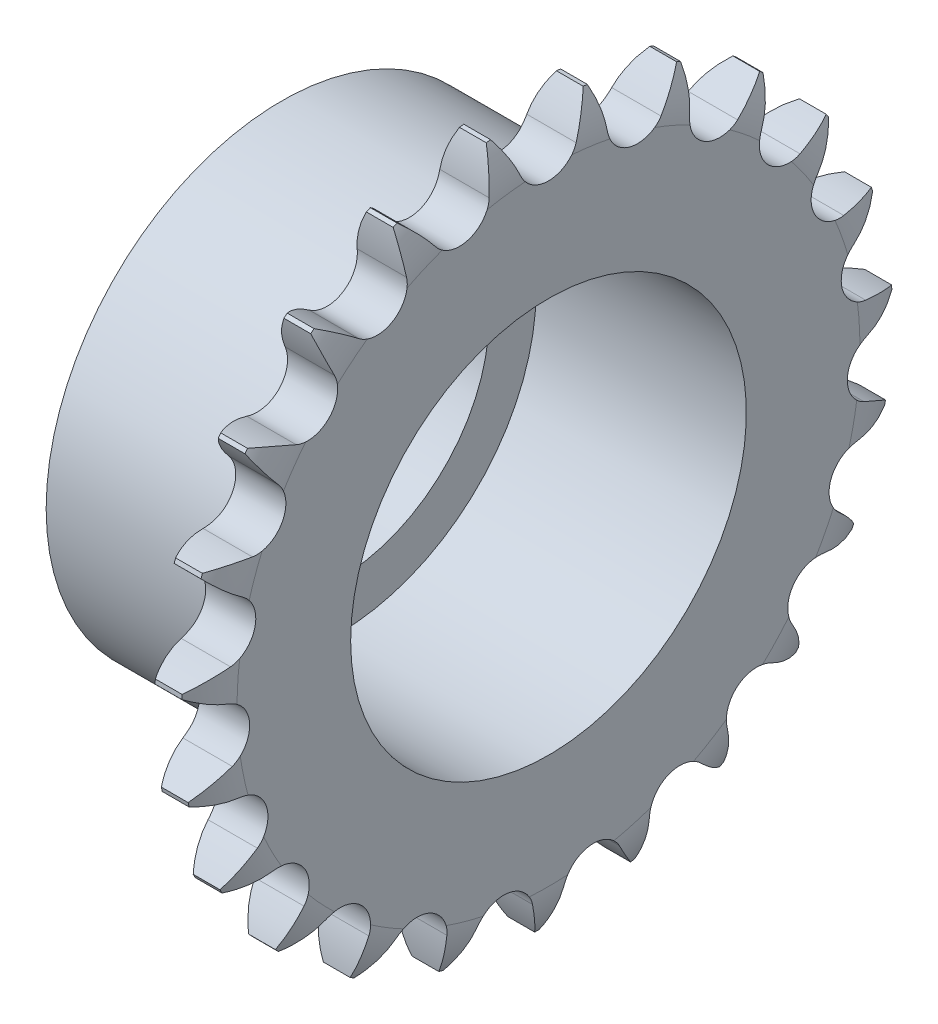
SolidWorks part; units mm, degrees
ref_plane "Plane1" through (0, 0, 0) normal (0, 0, 1) x (1, 0, 0)
ref_plane "Plane2" through (0, 0, 0) normal (0, 1, 0) x (1, 0, 0)
ref_plane "Plane3" through (0, 0, 0) normal (1, 0, 0) x (0, 0, -1)
sketch "Clipboard" plane through (0, 0, 0) normal (0, 1, 0) x (1, 0, 0)
  line L0 (0, 0) -> (8.7678, -3.7217)
  line L1 (-15, 0) -> (100, 0) construction
  line L2 (0, 0) -> (-0.8203, 0.9272)
  line L3 (0, 0) -> (-8.8973, 3.4006)
  line L4 (0, 0) -> (2.8536, 1.2113)
  line L5 (0, 0) -> (-15.9282, -5.9407)
  line L6 (0, 0) -> (-4.4098, -2.9753)
  line L7 (-0.8203, 0.9272) -> (14.7104, 7.8419)
  line L8 (-76.2, 38.1) -> (-72.9, 38.1)
  line L9 (-73.3242, 40.7328) -> (-72.926, 40.7699)
  line L10 (-73.4529, 9.1872) -> (-63.2129, 9.1872)
  circle A0 centre (0, 0) radius 3.175
  circle A1 centre (0, 0) radius 25
  circle A2 centre (0, 0) radius 25
  dimension "Dr" = 6.35
  dimension "MHD" = 50
  dimension "Hub_dia" = 50
  dimension "Num_teeth" = 23
  dimension "Pitch" = 9.525
  dimension "Width" = 3.1
  dimension "Side_relief" = 1.238
  dimension "Side_radius" = 9.525
  dimension "Overall_len" = 17
  dimension "Show_teeth" = 23
  dimension "Thickness" = 5.3196
  dimension "OAL" = 17.0005
  dimension "T_dim" = 3.3
  dimension "Fillet_rad" = 0.4
  dimension "Face_width" = 5.32
  dimension "Num_strands" = 1
  dimension "Transv_pitch" = 10.24
  dimension "Plate_wid" = 8.26
sketch "BasProSke" plane through (0, 0, 0) normal (0, 1, 0) x (1, 0, 0)
  line L0 (-10, 0) -> (60, 0) construction
  line L1 (0, 0) -> (0, 33.0578)
  line L2 (0, 0) -> (5.3196, 0)
  line L3 (5.3196, 0) -> (5.3196, 33.0578)
  line L4 (4.0816, 37.7536) -> (1.238, 37.7536)
  arc A0 (0, 33.0578) -> (1.238, 37.7536) centre (9.525, 33.0578) cw
  arc A1 (5.3196, 33.0578) -> (4.0816, 37.7536) centre (-4.2054, 33.0578) ccw
  dimension "Thickness" = 5.3196
  dimension "D1" = 9.525
  dimension "G1" = 1.238
  dimension "G2" = 1.238
  dimension "Diameter" = 75.5073
revolve "Base-Revolve" add sketch "BasProSke" angle 360 about L0
sketch "TooCutSke" plane through (0, 0, 0) normal (1, 0, 0) x (0, 0, -1)
  line L0 (0, 35.0073) -> (2.9742, 33.8083) construction
  line L1 (0, 0) -> (0, 107) construction
  line L2 (0, 35.0073) -> (-10, 35.0073) construction
  line L3 (0, 35.0073) -> (-2.9742, 33.8083) construction
  arc A0 (2.9742, 33.8083) -> (5.2383, 37.8933) centre (20.6424, 26.6854) cw
  arc A1 (2.9742, 33.8083) -> (-2.9742, 33.8083) centre (0, 35.0073) cw
  arc A2 (-2.9742, 33.8083) -> (-5.2383, 37.8933) centre (-20.6424, 26.6854) ccw
  arc A3 (5.2383, 37.8933) -> (-5.2383, 37.8933) centre (0, 0) ccw
  dimension "R1" = 3.2067
  dimension "R2" = 19.05
  dimension "Overcut" = 38.2536
  dimension "Seat_radius" = 35.0073
  dimension "X" = 136.087
extrude "ToothCut" cut sketch "TooCutSke" along normal through all
pattern_circular "TeethCuts" count 23 every 15.652 about axis through (-10, 0, 0) along (1, 0, 0) of "ToothCut"
sketch "HubNeaOneSke" plane through (0, 0, 0) normal (-1, 0, 0) x (0, 0, 1)
  circle A0 centre (0, 0) radius 25
  dimension "Diameter" = 50
extrude "HubNearOne" add sketch "HubNeaOneSke" along normal blind 23
fillet "HubNearOneFillet" radius 0.4 1 edges at (0, 0, -25)
sketch "HubNeaBotSke" plane through (0, 0, 0) normal (-1, 0, 0) x (0, 0, 1)
  circle A0 centre (0, 0) radius 25
  dimension "Diameter" = 50
extrude "HubNearBoth" [suppressed] add sketch "HubNeaBotSke" along normal blind 5.8404
fillet "HubNearBothFillet" [suppressed] radius 0.4
ref_plane "FarPln" through (5.3196, 0, 0) normal (1, 0, 0) x (0, 0, -1)
sketch "HubFarSke" plane through (5.3196, 0, 0) normal (1, 0, 0) x (0, 0, -1)
  circle A0 centre (0, 0) radius 25
  dimension "Diameter" = 50
extrude "HubFar" [suppressed] add sketch "HubFarSke" along normal blind 5.8404
fillet "HubFarFillet" [suppressed] radius 0.4
sketch "BorSke" plane through (0, 0, 0) normal (1, 0, 0) x (0, 0, -1)
  circle A0 centre (0, 0) radius 21
  dimension "Diameter" = 42
extrude "Bore" cut sketch "BorSke" along normal mid plane 34.001
sketch "KeySke" plane through (0, 0, 0) normal (1, 0, 0) x (0, 0, -1)
  line L0 (-6, 0) -> (-6, 24.3)
  line L1 (-6, 24.3) -> (6, 24.3)
  line L2 (6, 24.3) -> (6, 0)
  line L3 (0, 0) -> (0, 34) construction
  line L4 (-6, 0) -> (6, 0)
  dimension "Offset" = 24.3
  dimension "Width" = 12
extrude "Keyway" [suppressed] cut sketch "KeySke" along normal mid plane 34.001
pattern_circular "Keyway2" [suppressed] count 2 every 90 about axis through (-10, 0, 0) along (1, 0, 0)
sketch "Sketch1" plane through (-17.0005, 0, 0) normal (1, 0, 0) x (0, 0, -1)
  circle A0 centre (0, 0) radius 16
  dimension "D1" = 32
extrude "Cut-Extrude1" cut sketch "Sketch1" against normal up to next
equation "' \"Pitch@Clipboard\" = 12.7"
equation "' \"Num_strands@Clipboard\" = 1"
equation "' \"Num_teeth@Clipboard\" = 9"
equation "' \"Hub_dia@Clipboard\" = 50"
equation "' \"Overall_len@Clipboard\" = 3"
equation "' \"Diameter@BorSke\" = 12"
equation "' \"T_dim@Clipboard\" = 1"
equation "' \"Width@KeySke\" = 2"
equation "' \"Dr@Clipboard\" = 8.51"
equation "' \"Face_width@Clipboard\" = 7.2"
equation "' \"Side_radius@Clipboard\" = 12.7"
equation "' \"Side_relief@Clipboard\" = 1.27"
equation "' \"Transv_pitch@Clipboard\" = 13.92"
equation "' \"Show_teeth@Clipboard\" = 9"
equation "' \"Fillet_rad@Clipboard\" = 0.6"
equation "' \"Plate_wid@Clipboard\" = 11.8"
equation "\"Num_teeth@Clipboard\" = int( \"Num_teeth@Clipboard\" )"
equation "\"Num_teeth@Clipboard\" = ((sgn( \"Num_teeth@Clipboard\" - 5.0)+1)*( \"Num_teeth@Clipboard\" - 5.0))/2 +5.0"
equation "\"Num_teeth@Clipboard\" = ((sgn( \"Num_teeth@Clipboard\" - 200.0)-1)*( \"Num_teeth@Clipboard\" - 200.0))/-2 +200.0"
equation "\"MHD@Clipboard\" = \"Pitch@Clipboard\" * (1.0 / tan(3.14159265 / \"Num_teeth@Clipboard\" )) - 1.04 * \"Plate_wid@Clipboard\" - 0.76"
equation "\"Thickness@Clipboard\"  = \"Face_width@Clipboard\" + (\"Num_strands@Clipboard\" - 1) * \"Transv_pitch@Clipboard\""
equation "\"OAL@Clipboard\" = \"Thickness@Clipboard\" + 2 * \"Fillet_rad@Clipboard\" + 1"
equation "\"MHD@Clipboard\" = ((sgn( \"MHD@Clipboard\" - \"Hub_dia@Clipboard\" )-1)*( \"MHD@Clipboard\" - \"Hub_dia@Clipboard\" ))/-2+ \"Hub_dia@Clipboard\""
equation "\"OAL@Clipboard\" = ((sgn( \"OAL@Clipboard\" - \"Overall_len@Clipboard\" )+1)*( \"OAL@Clipboard\" - \"Overall_len@Clipboard\" ))/2 + \"Overall_len@Clipboard\" + 0.0005"
equation "\"Num_teeth@TeethCuts\" = int( \"Show_teeth@Clipboard\" ) + 1"
equation "\"Num_teeth@TeethCuts\" = ((sgn( \"Num_teeth@TeethCuts\" - \"Num_teeth@Clipboard\" )-1)*( \"Num_teeth@TeethCuts\" - \"Num_teeth@Clipboard\" ))/-2+ \"Num_teeth@Clipboard\""
equation "\"Num_teeth@TeethCuts\" = ((sgn( \"Num_teeth@TeethCuts\" - 2.0)+1)*( \"Num_teeth@TeethCuts\" - 2.0))/2 +2.0"
equation "\"Angle@TeethCuts\" = 360.0 / \"Num_teeth@Clipboard\""
equation "\"Seat_radius@TooCutSke\" = ( \"Pitch@Clipboard\" / 2.0) / sin(3.14159265 / \"Num_teeth@Clipboard\" ) - \"Dr@Clipboard\" / 2.0 + \"Dr@Clipboard\" * 0.505"
equation "\"R1@TooCutSke\"  = \"Dr@Clipboard\" * 0.505"
equation "\"X@TooCutSke\" = 140.0 - (90.0 / \"Num_teeth@Clipboard\")"
equation "\"R2@TooCutSke\" = 0.12 * \"Dr@Clipboard\" * ( \"Num_teeth@Clipboard\" + 2.0)"
equation "\"Overcut@TooCutSke\" = 0.5 + 0.625 * \"Pitch@Clipboard\" - 0.5 * \"Dr@Clipboard\"  +  \"Pitch@Clipboard\" / 2.0 / sin(3.14159265 / \"Num_teeth@Clipboard\" )"
equation "\"Diameter@BasProSke\" = 2.0 * ( 0.625 * \"Pitch@Clipboard\" - 0.5 * \"Dr@Clipboard\"  +  \"Pitch@Clipboard\" / 2.0 / sin(3.14159265 / \"Num_teeth@Clipboard\" ))"
equation "\"Thickness@BasProSke\"  = \"Thickness@Clipboard\""
equation "\"G1@BasProSke\" =  \"Side_relief@Clipboard\""
equation "\"G2@BasProSke\" =  \"Side_relief@Clipboard\""
equation "\"D1@BasProSke\" =  \"Side_radius@Clipboard\""
equation "\"Diameter@HubNeaOneSke\" = \"MHD@Clipboard\""
equation "\"Length@HubNearOne\"=23"
equation "\"Diameter@HubNeaBotSke\" = \"MHD@Clipboard\""
equation "\"Length@HubNearBoth\" = ( \"OAL@Clipboard\" - \"Thickness@BasProSke\" ) / 2.0"
equation "\"D1@HubNearOneFillet\" = \"Fillet_rad@Clipboard\""
equation "\"D1@HubNearBothFillet\" = \"Fillet_rad@Clipboard\""
equation "\"Thickness@FarPln\" = \"Thickness@BasProSke\""
equation "\"Diameter@HubFarSke\" = \"MHD@Clipboard\""
equation "\"Length@HubFar\" = ( \"OAL@Clipboard\" - \"Thickness@BasProSke\" ) / 2.0"
equation "\"D1@HubFarFillet\" = \"Fillet_rad@Clipboard\""
equation "\"D1@Bore\" = \"OAL@Clipboard\" * 2.0"
equation "\"D1@Keyway\" = \"OAL@Clipboard\" * 2.0"
equation "\"Offset@KeySke\" = \"T_dim@Clipboard\" + \"Diameter@BorSke\" / 2.0"
